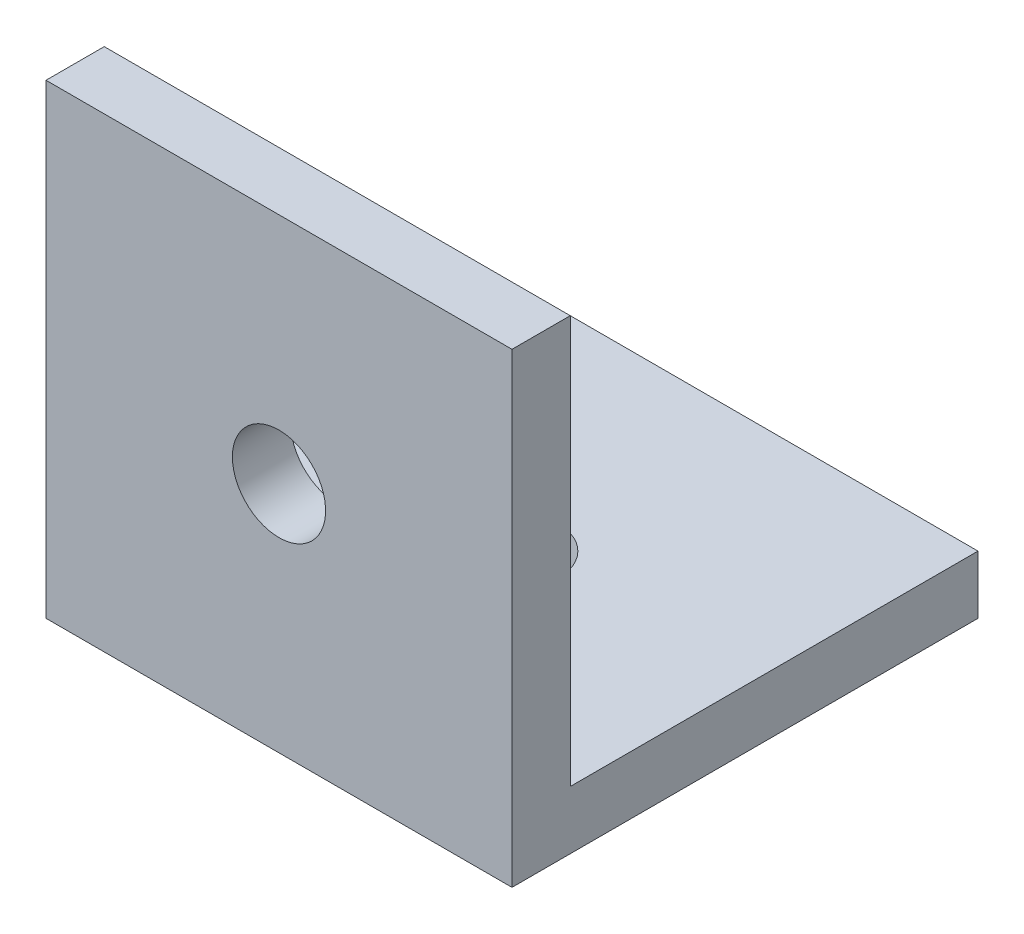
SolidWorks part; units mm, degrees
ref_plane "Front Plane" through (0, 0, 0) normal (0, 0, 1) x (1, 0, 0)
ref_plane "Top Plane" through (0, 0, 0) normal (0, 1, 0) x (1, 0, 0)
ref_plane "Right Plane" through (0, 0, 0) normal (1, 0, 0) x (0, 0, -1)
sketch "Sketch4" plane through (0, 0, 0) normal (0, 0, 1) x (1, 0, 0)
  line L1 (12.7, -12.7) -> (-12.7, -12.7)
  line L2 (12.7, -12.7) -> (12.7, 12.7)
  line L3 (12.7, 12.7) -> (-12.7, 12.7)
  line L4 (-12.7, -12.7) -> (-12.7, 12.7)
  line L5 (12.7, -12.7) -> (-12.7, 12.7) construction
  line L6 (12.7, 12.7) -> (-12.7, -12.7) construction
  point P0 (0, 0)
extrude "Boss-Extrude3" add sketch "Sketch4" along normal blind 3.175
sketch "Sketch5" plane through (0, 0, 0) normal (0, 0, -1) x (-1, 0, 0)
  line L0 (12.7, 12.7) -> (12.7, -12.7) construction
  line L1 (12.7, -12.7) -> (-12.7, -12.7) construction
  line L2 (12.7, -9.525) -> (-12.7, -9.525)
  line L3 (12.7, -9.525) -> (12.7, -12.7)
  line L4 (12.7, -12.7) -> (-12.7, -12.7)
  line L5 (-12.7, -9.525) -> (-12.7, -12.7)
  line L6 (-12.7, -12.7) -> (-12.7, 12.7) construction
  dimension "D1" = 0
  dimension "D2" = 0
extrude "Boss-Extrude4" add sketch "Sketch5" along normal blind 22.225
sketch "Sketch6" plane through (0, -9.525, 0) normal (0, 1, 0) x (1, 0, 0)
  line L0 (0, 0) -> (0, 22.225) construction
  line L1 (-12.7, 22.225) -> (12.7, 22.225) construction
  circle A0 centre (0, 9.525) radius 2.54
  dimension "D1" = 5.08
  dimension "D2" = 12.7
extrude "Cut-Extrude1" cut sketch "Sketch6" against normal through all
sketch "Sketch7" plane through (0, 0, 0) normal (0, 0, -1) x (-1, 0, 0)
  line L0 (-12.7, -9.525) -> (-12.7, 12.7) construction
  line L1 (-12.7, 12.7) -> (12.7, 12.7) construction
  circle A0 centre (0, 0) radius 2.54
  dimension "D1" = 12.7
  dimension "D3" = 5.08
  dimension "D2" = 12.7
extrude "Cut-Extrude2" cut sketch "Sketch7" against normal through all
